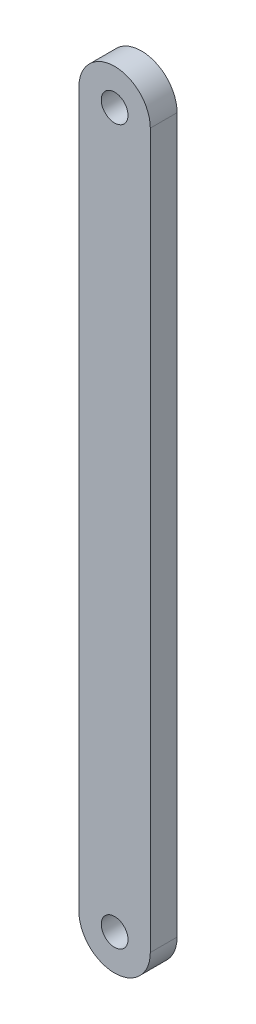
SolidWorks part; units mm, degrees
ref_plane "前基準面" through (0, 0, 0) normal (0, 0, 1) x (1, 0, 0)
ref_plane "上基準面" through (0, 0, 0) normal (0, 1, 0) x (1, 0, 0)
ref_plane "右基準面" through (0, 0, 0) normal (1, 0, 0) x (0, 0, -1)
sketch "Model" plane through (0, 0, 0) normal (0, 0, 1) x (1, 0, 0)
  line L0 (2360.94, 1556.087) -> (2341.94, 1556.087)
  line L1 (2282.5841, 1545.083) -> (2265.648, 1562.019)
  line L2 (2264.9409, 1562.7262) -> (2257.2918, 1570.3752)
  line L3 (2291.9966, 1535.6704) -> (2283.2912, 1544.3759)
  line L4 (2383.2394, 1583.0851) -> (2383.2394, 1591.0855)
  line L5 (2368.4402, 1574.6001) -> (2368.4402, 1566.6001)
  line L6 (2368.4402, 1577.0864) -> (2368.4402, 1575.6001)
  line L7 (2250.4404, 1612.885) -> (2250.4405, 1634.8001)
  line L8 (2250.4403, 1591.1001) -> (2250.4404, 1611.885)
  line L9 (2265.9406, 1588.1) -> (2240.9406, 1588.1001)
  line L10 (2297.9406, 1588.0998) -> (2266.9406, 1588.1)
  line L11 (2190.4406, 1631.8177) -> (2190.4404, 1591.9877)
  line L12 (2190.7401, 1515.6239) -> (2190.7401, 1497.1002)
  line L13 (2190.7401, 1540.2506) -> (2190.7401, 1516.6239)
  line L14 (2190.7401, 1571.1544) -> (2190.7401, 1541.2506)
  line L15 (2190.7401, 1577.1001) -> (2190.7401, 1572.1544)
  line L16 (2198.7401, 1541.6001) -> (2198.7401, 1516.9664)
  line L17 (2198.7401, 1571.0862) -> (2198.7401, 1542.6001)
  line L18 (2206.7401, 1563.7416) -> (2206.7401, 1542.6001)
  line L19 (2206.7401, 1541.6001) -> (2206.7401, 1517.1445)
  line L20 (2367.7339, 1622.5881) -> (2377.2848, 1622.5881)
  line L21 (2378.2848, 1622.5881) -> (2380.2436, 1622.5881)
  line L22 (2170.7403, 1546.4261) -> (2170.7403, 1568.4955)
  line L23 (2170.7403, 1514.0747) -> (2170.7403, 1545.4261)
  line L24 (2182.7403, 1561.7113) -> (2182.7403, 1543.3225)
  line L25 (2182.7403, 1542.3225) -> (2182.7403, 1512.6855)
  line L26 (2402.8405, 1640.5213) -> (2432.7394, 1640.5232)
  line L27 (2310.4404, 1591.078) -> (2310.4432, 1595.6001)
  line L28 (2190.4406, 1634.8004) -> (2190.4406, 1631.8007)
  line L29 (2383.2395, 1620.7452) -> (2383.2395, 1632.084)
  line L30 (2383.2394, 1600.086) -> (2383.2394, 1612.086)
  line L31 (2428.4388, 1546.995) -> (2428.4388, 1524.6001)
  line L32 (2431.4402, 1556.6798) -> (2431.4402, 1567.4449)
  line L33 (2364.4522, 1580.086) -> (2373.94, 1580.086)
  line L34 (2206.7401, 1497.1001) -> (2206.7401, 1516.1445)
  line L35 (2282.8042, 1526.478) -> (2278.5615, 1522.2355)
  line L36 (2278.5615, 1522.2355) -> (2243.8568, 1556.9402)
  line L37 (2243.8568, 1556.9402) -> (2248.0994, 1561.1828)
  line L38 (2248.0994, 1561.1828) -> (2250.2208, 1559.0615)
  line L39 (2250.2208, 1559.0615) -> (2251.635, 1560.4757)
  line L40 (2251.635, 1560.4757) -> (2253.7563, 1558.3544)
  line L41 (2253.7563, 1558.3544) -> (2252.8371, 1557.4352)
  line L42 (2252.8371, 1557.4352) -> (2254.6048, 1555.6674)
  line L43 (2254.6048, 1555.6674) -> (2255.5241, 1556.5867)
  line L44 (2255.5241, 1556.5867) -> (2268.6055, 1543.5052)
  line L45 (2268.6055, 1543.5052) -> (2270.7269, 1545.6265)
  line L46 (2270.7269, 1545.6265) -> (2257.6454, 1558.708)
  line L47 (2257.6454, 1558.708) -> (2258.5646, 1559.6272)
  line L48 (2258.5646, 1559.6272) -> (2256.7968, 1561.395)
  line L49 (2256.7968, 1561.395) -> (2255.8776, 1560.4757)
  line L50 (2255.8776, 1560.4757) -> (2253.7563, 1562.5971)
  line L51 (2253.7563, 1562.5971) -> (2255.1705, 1564.0113)
  line L52 (2255.1705, 1564.0113) -> (2253.0492, 1566.1326)
  line L53 (2253.0492, 1566.1326) -> (2264.3629, 1577.4463)
  line L54 (2264.3629, 1577.4463) -> (2299.0677, 1542.7415)
  line L55 (2299.0677, 1542.7415) -> (2287.754, 1531.4278)
  line L56 (2287.754, 1531.4278) -> (2285.6327, 1533.5491)
  line L57 (2285.6327, 1533.5491) -> (2284.2184, 1532.1349)
  line L58 (2284.2184, 1532.1349) -> (2281.39, 1534.9633)
  line L59 (2281.39, 1534.9633) -> (2282.3093, 1535.8826)
  line L60 (2282.3093, 1535.8826) -> (2280.5415, 1537.6503)
  line L61 (2280.5415, 1537.6503) -> (2279.6223, 1536.7311)
  line L62 (2279.6223, 1536.7311) -> (2279.198, 1537.1554)
  line L63 (2279.198, 1537.1554) -> (2277.0767, 1535.034)
  line L64 (2277.0767, 1535.034) -> (2277.5009, 1534.6098)
  line L65 (2277.5009, 1534.6098) -> (2276.5817, 1533.6905)
  line L66 (2276.5817, 1533.6905) -> (2278.3495, 1531.9228)
  line L67 (2278.3495, 1531.9228) -> (2279.2687, 1532.842)
  line L68 (2279.2687, 1532.842) -> (2282.0971, 1530.0136)
  line L69 (2282.0971, 1530.0136) -> (2280.6829, 1528.5994)
  line L70 (2280.6829, 1528.5994) -> (2282.8042, 1526.478)
  line L71 (2420.0943, 1572.5771) -> (2403.5521, 1576.8112)
  line L72 (2396.9173, 1574.0826) -> (2384.4348, 1577.0916)
  line L73 (2384.4348, 1577.0916) -> (2379.9348, 1577.0881)
  line L74 (2379.9348, 1577.0881) -> (2379.9325, 1580.0881)
  line L75 (2368.4399, 1561.1801) -> (2381.9283, 1561.1801)
  line L76 (2381.9283, 1561.1801) -> (2395.958, 1562.2789)
  line L77 (2402.0756, 1571.0841) -> (2418.6076, 1566.7642)
  line L78 (2425.3801, 1562.2877) -> (2412.2591, 1562.287)
  line L79 (2412.2591, 1562.287) -> (2394.365, 1560.187)
  line L80 (2394.365, 1552.187) -> (2412.3649, 1550.087)
  line L81 (2412.3649, 1550.087) -> (2420.94, 1550.087)
  line L82 (2335.4379, 1586.1907) -> (2341.4379, 1586.1907)
  line L83 (2341.4379, 1586.1907) -> (2341.4379, 1583.1907)
  line L84 (2341.4379, 1583.1907) -> (2353.4379, 1583.1907)
  line L85 (2353.4379, 1583.1907) -> (2353.4379, 1586.1907)
  line L86 (2353.4379, 1586.1907) -> (2359.4375, 1586.1907)
  line L87 (2256.2117, 1499.3305) -> (2276.7178, 1519.8366)
  line L88 (2421.94, 1550.087) -> (2426.9388, 1550.087)
  line L89 (2426.9388, 1550.087) -> (2426.9388, 1547.087)
  line L90 (2426.9388, 1547.087) -> (2428.4388, 1547.087)
  line L91 (2361.94, 1556.087) -> (2374.4388, 1556.087)
  line L92 (2374.4388, 1556.087) -> (2374.4388, 1547.087)
  line L93 (2374.4388, 1547.087) -> (2381.9388, 1547.087)
  line L94 (2381.9388, 1547.087) -> (2381.9388, 1550.087)
  line L95 (2381.9388, 1550.087) -> (2391.9388, 1550.087)
  line L96 (2391.9388, 1550.087) -> (2391.9388, 1547.087)
  line L97 (2391.9388, 1547.087) -> (2402.9388, 1547.087)
  line L98 (2402.9388, 1547.087) -> (2402.9388, 1543.0871)
  line L99 (2402.9388, 1543.0871) -> (2401.6388, 1543.0871)
  line L100 (2401.6388, 1543.0871) -> (2401.6388, 1540.5871)
  line L101 (2401.6388, 1540.5871) -> (2402.9388, 1540.5871)
  line L102 (2402.9388, 1540.5871) -> (2402.9388, 1539.087)
  line L103 (2402.9388, 1539.087) -> (2405.9388, 1539.087)
  line L104 (2405.9388, 1539.087) -> (2405.9388, 1540.5871)
  line L105 (2405.9388, 1540.5871) -> (2407.2388, 1540.5871)
  line L106 (2407.2388, 1540.5871) -> (2407.2388, 1543.0871)
  line L107 (2407.2388, 1543.0871) -> (2405.9388, 1543.0871)
  line L108 (2405.9388, 1543.0871) -> (2405.9388, 1547.087)
  line L109 (2405.9388, 1547.087) -> (2416.9388, 1547.087)
  line L110 (2416.9388, 1547.087) -> (2416.9388, 1550.087)
  line L111 (2310.4464, 1608.3582) -> (2310.467, 1633.5996)
  line L112 (2310.467, 1633.5996) -> (2310.4412, 1635.1138)
  line L113 (2307.986, 1637.7498) -> (2259.9155, 1646.6381)
  line L114 (2255.7293, 1644.7139) -> (2253.9054, 1641.5736)
  line L115 (2359.4374, 1588.5921) -> (2353.4373, 1588.5916)
  line L116 (2353.4373, 1588.5916) -> (2353.4371, 1591.5917)
  line L117 (2352.2968, 1593.5664) -> (2355.8453, 1599.714)
  line L118 (2353.2044, 1605.1909) -> (2347.3559, 1595.0085)
  line L119 (2341.4371, 1591.5907) -> (2341.4374, 1588.5906)
  line L120 (2341.4374, 1588.5906) -> (2335.4373, 1588.5901)
  line L121 (2359.4375, 1586.8452) -> (2359.4375, 1583.0846)
  line L122 (2362.3378, 1580.086) -> (2363.4522, 1580.086)
  line L123 (2374.94, 1580.086) -> (2380.1389, 1580.086)
  line L124 (2434.3958, 1580.0881) -> (2452.2402, 1580.0881)
  line L125 (2452.2402, 1580.0881) -> (2452.2402, 1572.0881)
  line L126 (2452.2402, 1572.0881) -> (2449.2402, 1572.0881)
  line L127 (2449.2402, 1572.0881) -> (2449.2402, 1559.5881)
  line L128 (2449.2402, 1559.5881) -> (2445.2402, 1559.5881)
  line L129 (2445.2402, 1559.5881) -> (2445.2402, 1560.8881)
  line L130 (2445.2402, 1560.8881) -> (2442.2402, 1560.8881)
  line L131 (2442.2402, 1560.8881) -> (2442.2402, 1559.5881)
  line L132 (2442.2402, 1559.5881) -> (2440.2402, 1559.5881)
  line L133 (2440.2402, 1559.5881) -> (2440.2402, 1556.5881)
  line L134 (2440.2402, 1556.5881) -> (2442.2402, 1556.5881)
  line L135 (2442.2402, 1556.5881) -> (2442.2402, 1555.2881)
  line L136 (2442.2402, 1555.2881) -> (2445.2402, 1555.2881)
  line L137 (2445.2402, 1555.2881) -> (2445.2402, 1556.5881)
  line L138 (2445.2402, 1556.5881) -> (2449.2402, 1556.5881)
  line L139 (2449.2402, 1556.5881) -> (2449.2402, 1542.0881)
  line L140 (2449.2402, 1542.0881) -> (2452.2402, 1542.0881)
  line L141 (2452.2402, 1542.0881) -> (2452.2402, 1533.0881)
  line L142 (2452.2402, 1533.0881) -> (2449.0167, 1533.0881)
  line L143 (2445.0402, 1526.0881) -> (2445.0402, 1520.0881)
  line L144 (2445.0402, 1520.0881) -> (2428.4388, 1520.0881)
  line L145 (2386.4827, 1580.0881) -> (2433.3958, 1580.0881)
  line L146 (2368.4378, 1573.3291) -> (2372.4378, 1573.3322)
  line L147 (2372.4378, 1573.3322) -> (2372.4368, 1574.5822)
  line L148 (2372.4368, 1574.5822) -> (2374.9293, 1574.5842)
  line L149 (2374.9293, 1574.5842) -> (2374.9303, 1573.3342)
  line L150 (2374.9303, 1573.3342) -> (2376.9303, 1573.3358)
  line L151 (2376.9303, 1573.3358) -> (2376.9327, 1570.3358)
  line L152 (2376.9327, 1570.3358) -> (2374.9327, 1570.3342)
  line L153 (2374.9327, 1570.3342) -> (2374.9337, 1569.0842)
  line L154 (2374.9337, 1569.0842) -> (2372.4337, 1569.0822)
  line L155 (2372.4337, 1569.0822) -> (2372.4327, 1570.3322)
  line L156 (2372.4327, 1570.3322) -> (2368.4402, 1570.3291)
  line L157 (2238.534, 1517.0082) -> (2259.0401, 1537.5143)
  line L158 (2241.3624, 1555.1919) -> (2220.8563, 1534.6858)
  line L159 (2428.4402, 1527.5881) -> (2431.4402, 1527.5881)
  line L160 (2431.4402, 1527.5881) -> (2431.4402, 1540.5881)
  line L161 (2431.4402, 1540.5881) -> (2435.4402, 1540.5881)
  line L162 (2435.4402, 1540.5881) -> (2435.4402, 1539.2881)
  line L163 (2435.4402, 1539.2881) -> (2438.4402, 1539.2881)
  line L164 (2438.4402, 1539.2881) -> (2438.4402, 1540.5881)
  line L165 (2438.4402, 1540.5881) -> (2440.4402, 1540.5881)
  line L166 (2440.4402, 1540.5881) -> (2440.4402, 1543.5881)
  line L167 (2440.4402, 1543.5881) -> (2438.4402, 1543.5881)
  line L168 (2438.4402, 1543.5881) -> (2438.4402, 1544.8881)
  line L169 (2438.4402, 1544.8881) -> (2435.4402, 1544.8881)
  line L170 (2435.4402, 1544.8881) -> (2435.4402, 1543.5881)
  line L171 (2435.4402, 1543.5881) -> (2431.4402, 1543.5881)
  line L172 (2431.4402, 1543.5881) -> (2431.4402, 1555.6798)
  line L173 (2431.4402, 1568.4449) -> (2431.4402, 1575.0881)
  line L174 (2431.4402, 1575.0881) -> (2428.4402, 1575.0881)
  line L175 (2428.4402, 1575.0881) -> (2428.4402, 1580.0881)
  line L176 (2257.9403, 1595.8) -> (2257.9403, 1598.8)
  line L177 (2257.9403, 1598.8) -> (2267.9403, 1598.8)
  line L178 (2267.9403, 1598.8) -> (2267.9403, 1595.8)
  line L179 (2267.9403, 1595.8) -> (2257.9403, 1595.8)
  line L180 (2260.6167, 1627.8) -> (2260.6166, 1617.8)
  line L181 (2260.6166, 1617.8) -> (2257.6166, 1617.8001)
  line L182 (2257.6166, 1617.8001) -> (2257.6167, 1627.8001)
  line L183 (2257.6167, 1627.8001) -> (2260.6167, 1627.8)
  line L184 (2240.2641, 1598.1001) -> (2240.2642, 1608.1001)
  line L185 (2240.2642, 1608.1001) -> (2243.2642, 1608.1001)
  line L186 (2243.2642, 1608.1001) -> (2243.2641, 1598.1001)
  line L187 (2243.2641, 1598.1001) -> (2240.2641, 1598.1001)
  line L188 (2158.7403, 1580.4001) -> (2158.7403, 1500.4)
  line L189 (2170.7403, 1500.4) -> (2170.7403, 1513.0747)
  line L190 (2170.7403, 1569.4955) -> (2170.7403, 1580.4)
  line L191 (2368.4348, 1577.079) -> (2369.9348, 1577.0802)
  line L192 (2369.9348, 1577.0802) -> (2369.9325, 1580.0802)
  line L193 (2242.4043, 1648.5707) -> (2168.1294, 1646.9241)
  line L194 (2168.7764, 1638.795) -> (2186.8708, 1638.8729)
  line L195 (2186.8708, 1638.8729) -> (2242.5211, 1639.1123)
  line L196 (2410.365, 1556.937) -> (2415.365, 1556.937)
  line L197 (2415.365, 1555.437) -> (2410.365, 1555.437)
  line L198 (2304.4403, 1614.7998) -> (2307.4404, 1614.7998)
  line L199 (2307.4404, 1614.7998) -> (2307.4403, 1608.7998)
  line L200 (2307.4403, 1608.7998) -> (2304.4403, 1608.7998)
  line L201 (2304.4403, 1608.7998) -> (2304.4403, 1614.7998)
  line L202 (2301.4404, 1631.7998) -> (2278.4404, 1631.7999)
  line L203 (2278.4404, 1631.7999) -> (2278.4404, 1619.7999)
  line L204 (2278.4404, 1619.7999) -> (2301.4404, 1619.7998)
  line L205 (2301.4404, 1619.7998) -> (2301.4404, 1631.7998)
  line L206 (2307.4403, 1601.7998) -> (2307.4403, 1595.7998)
  line L207 (2307.4403, 1595.7998) -> (2304.4403, 1595.7998)
  line L208 (2304.4403, 1595.7998) -> (2304.4403, 1601.7998)
  line L209 (2304.4403, 1601.7998) -> (2307.4403, 1601.7998)
  line L210 (2302.9403, 1595.7998) -> (2302.9403, 1598.7998)
  line L211 (2302.9403, 1598.7998) -> (2292.9403, 1598.7999)
  line L212 (2292.9403, 1598.7999) -> (2292.9403, 1595.7999)
  line L213 (2292.9403, 1595.7999) -> (2302.9403, 1595.7998)
  line L214 (2239.9406, 1588.1001) -> (2193.4403, 1588.1004)
  line L215 (2190.4403, 1591.1004) -> (2190.4404, 1591.9877)
  line L216 (2253.4032, 1640.7089) -> (2250.8464, 1636.3069)
  line L217 (2246.9406, 1637.8001) -> (2193.4406, 1637.8004)
  line L218 (2190.4406, 1634.8004) -> (2190.4406, 1634.8033)
  line L219 (2242.9405, 1630.1001) -> (2232.9405, 1630.1002)
  line L220 (2232.9405, 1630.1002) -> (2232.9405, 1627.1002)
  line L221 (2232.9405, 1627.1002) -> (2242.9405, 1627.1001)
  line L222 (2242.9405, 1627.1001) -> (2242.9405, 1630.1001)
  line L223 (2207.9405, 1630.1003) -> (2197.9405, 1630.1004)
  line L224 (2197.9405, 1630.1004) -> (2197.9405, 1627.1004)
  line L225 (2197.9405, 1627.1004) -> (2207.9405, 1627.1003)
  line L226 (2207.9405, 1627.1003) -> (2207.9405, 1630.1003)
  line L227 (2222.4404, 1606.1002) -> (2199.4404, 1606.1003)
  line L228 (2199.4404, 1606.1003) -> (2199.4404, 1594.1003)
  line L229 (2199.4404, 1594.1003) -> (2222.4404, 1594.1002)
  line L230 (2222.4404, 1594.1002) -> (2222.4404, 1606.1002)
  line L231 (2196.4405, 1624.1004) -> (2193.4405, 1624.1004)
  line L232 (2193.4405, 1624.1004) -> (2193.4405, 1630.1004)
  line L233 (2193.4405, 1630.1004) -> (2196.4405, 1630.1004)
  line L234 (2196.4405, 1630.1004) -> (2196.4405, 1624.1004)
  line L235 (2196.4404, 1611.1004) -> (2193.4404, 1611.1004)
  line L236 (2193.4404, 1611.1004) -> (2193.4405, 1617.1004)
  line L237 (2193.4405, 1617.1004) -> (2196.4405, 1617.1004)
  line L238 (2196.4405, 1617.1004) -> (2196.4404, 1611.1004)
  line L239 (2320.4402, 1592.1001) -> (2316.9402, 1592.1001)
  line L240 (2316.9402, 1592.1001) -> (2316.9402, 1569.1001)
  line L241 (2316.9402, 1569.1001) -> (2328.9402, 1569.1001)
  line L242 (2328.9402, 1569.1001) -> (2328.9402, 1592.1001)
  line L243 (2328.9402, 1592.1001) -> (2325.4402, 1592.1001)
  line L244 (2325.4402, 1592.1001) -> (2325.4402, 1594.1002)
  line L245 (2325.4402, 1594.1002) -> (2320.4402, 1594.1002)
  line L246 (2320.4402, 1594.1002) -> (2320.4402, 1592.1001)
  line L247 (2251.2619, 1508.5229) -> (2253.7368, 1506.048)
  line L248 (2253.7368, 1506.048) -> (2270.0002, 1522.3115)
  line L249 (2270.0002, 1522.3115) -> (2261.515, 1530.7968)
  line L250 (2261.515, 1530.7968) -> (2245.2515, 1514.5333)
  line L251 (2245.2515, 1514.5333) -> (2247.7264, 1512.0584)
  line L252 (2247.7264, 1512.0584) -> (2246.3121, 1510.6441)
  line L253 (2246.3121, 1510.6441) -> (2249.8476, 1507.1086)
  line L254 (2249.8476, 1507.1086) -> (2251.2619, 1508.5229)
  line L255 (2233.5842, 1526.2006) -> (2236.0591, 1523.7257)
  line L256 (2236.0591, 1523.7257) -> (2252.3226, 1539.9891)
  line L257 (2252.3226, 1539.9891) -> (2243.8373, 1548.4744)
  line L258 (2243.8373, 1548.4744) -> (2227.5738, 1532.211)
  line L259 (2227.5738, 1532.211) -> (2230.0487, 1529.7361)
  line L260 (2230.0487, 1529.7361) -> (2228.6344, 1528.3218)
  line L261 (2228.6344, 1528.3218) -> (2232.17, 1524.7863)
  line L262 (2232.17, 1524.7863) -> (2233.5842, 1526.2006)
  line L263 (2198.7401, 1515.9664) -> (2198.7401, 1497.1001)
  line L264 (2198.7401, 1572.0862) -> (2198.7401, 1577.1001)
  line L265 (2175.2403, 1516.6002) -> (2175.2403, 1509.1002)
  line L266 (2175.2403, 1509.1002) -> (2178.2403, 1509.1002)
  line L267 (2178.2403, 1509.1002) -> (2178.2403, 1516.6002)
  line L268 (2178.2403, 1516.6002) -> (2175.2403, 1516.6002)
  line L269 (2175.2403, 1569.1002) -> (2175.2403, 1564.1002)
  line L270 (2175.2403, 1564.1002) -> (2178.2403, 1564.1002)
  line L271 (2178.2403, 1564.1002) -> (2178.2403, 1569.1002)
  line L272 (2178.2403, 1569.1002) -> (2175.2403, 1569.1002)
  line L273 (2163.2403, 1562.4) -> (2166.2403, 1562.4)
  line L274 (2166.2403, 1562.4) -> (2166.2403, 1570.4)
  line L275 (2166.2403, 1570.4) -> (2163.2403, 1570.4)
  line L276 (2163.2403, 1570.4) -> (2163.2403, 1562.4)
  line L277 (2163.2403, 1532.4) -> (2166.2403, 1532.4)
  line L278 (2166.2403, 1532.4) -> (2166.2403, 1523.4)
  line L279 (2166.2403, 1523.4) -> (2163.2403, 1523.4)
  line L280 (2163.2403, 1523.4) -> (2163.2403, 1532.4)
  line L281 (2182.7403, 1562.7113) -> (2182.7403, 1579.1002)
  line L282 (2182.7403, 1511.6855) -> (2182.7403, 1499.1001)
  line L283 (2206.7401, 1564.7416) -> (2206.7401, 1577.1001)
  line L284 (2434.7402, 1574.5881) -> (2434.7402, 1566.3381)
  line L285 (2436.7402, 1564.3382) -> (2443.7402, 1564.3382)
  line L286 (2445.7402, 1566.3381) -> (2445.7402, 1574.5881)
  line L287 (2443.2402, 1577.0881) -> (2437.2402, 1577.0881)
  line L288 (2271.2218, 1535.9391) -> (2278.2928, 1543.0101)
  line L289 (2278.2928, 1543.0101) -> (2276.1715, 1545.1315)
  line L290 (2276.1715, 1545.1315) -> (2269.1005, 1538.0605)
  line L291 (2269.1005, 1538.0605) -> (2271.2218, 1535.9391)
  line L292 (2163.9903, 1515.4) -> (2163.9903, 1510.4)
  line L293 (2165.4903, 1510.4) -> (2165.4903, 1515.4)
  line L294 (2277.9403, 1606.8) -> (2277.9403, 1600.8)
  line L295 (2277.9403, 1600.8) -> (2267.9403, 1600.8)
  line L296 (2267.9403, 1600.8) -> (2267.9403, 1606.8)
  line L297 (2267.9403, 1606.8) -> (2277.9403, 1606.8)
  line L298 (2313.4402, 1563.1001) -> (2332.4402, 1563.1001)
  line L299 (2335.4402, 1566.1001) -> (2335.4402, 1569.6001)
  line L300 (2335.4402, 1570.6001) -> (2335.4402, 1595.1001)
  line L301 (2332.4402, 1598.1001) -> (2320.9401, 1598.1001)
  line L302 (2310.4402, 1595.1001) -> (2310.4402, 1578.1001)
  line L303 (2365.2395, 1629.0842) -> (2365.2394, 1632.0842)
  line L304 (2365.2394, 1632.0842) -> (2359.2394, 1632.0842)
  line L305 (2359.2394, 1632.0842) -> (2359.2394, 1634.4843)
  line L306 (2359.2394, 1634.4843) -> (2365.2394, 1634.4842)
  line L307 (2365.2394, 1634.4842) -> (2365.2396, 1637.4843)
  line L308 (2365.2396, 1637.4843) -> (2377.2395, 1637.4841)
  line L309 (2377.2395, 1637.4841) -> (2377.2395, 1634.484)
  line L310 (2377.2395, 1634.484) -> (2383.2395, 1634.484)
  line L311 (2377.2388, 1594.586) -> (2377.2388, 1617.386)
  line L312 (2377.2388, 1617.386) -> (2365.2379, 1617.386)
  line L313 (2365.2379, 1617.386) -> (2365.2379, 1594.586)
  line L314 (2365.2379, 1594.586) -> (2377.2388, 1594.586)
  line L315 (2419.5574, 1621.7062) -> (2407.3574, 1621.7062)
  line L316 (2407.3574, 1621.7062) -> (2407.3574, 1598.9062)
  line L317 (2407.3574, 1598.9062) -> (2419.5574, 1598.9062)
  line L318 (2419.5574, 1598.9062) -> (2419.5574, 1621.7062)
  line L319 (2363.4402, 1570.6886) -> (2364.9402, 1570.6886)
  line L320 (2364.9402, 1570.6886) -> (2364.9402, 1565.6886)
  line L321 (2364.9402, 1565.6886) -> (2363.4402, 1565.6886)
  line L322 (2363.4402, 1565.6886) -> (2363.4402, 1561.9886)
  line L323 (2363.4402, 1561.9886) -> (2340.6402, 1561.9886)
  line L324 (2340.6402, 1561.9886) -> (2340.6402, 1574.1886)
  line L325 (2340.6402, 1574.1886) -> (2363.4402, 1574.1886)
  line L326 (2363.4402, 1574.1886) -> (2363.4402, 1570.6886)
  line L327 (2383.2394, 1592.0855) -> (2383.2394, 1600.086)
  line L328 (2383.2394, 1600.086) -> (2380.2394, 1600.086)
  line L329 (2380.2394, 1600.086) -> (2380.2394, 1612.086)
  line L330 (2380.2394, 1612.086) -> (2383.2394, 1612.086)
  line L331 (2383.2394, 1612.086) -> (2383.2394, 1615.4156)
  line L332 (2443.6753, 1583.3062) -> (2443.6753, 1637.3063)
  line L333 (2359.4375, 1619.7446) -> (2359.4375, 1612.086)
  line L334 (2359.4375, 1612.086) -> (2362.4378, 1612.086)
  line L335 (2362.4378, 1612.086) -> (2362.4378, 1600.086)
  line L336 (2362.4378, 1600.086) -> (2359.4375, 1600.086)
  line L337 (2359.4375, 1600.086) -> (2359.4375, 1587.8452)
  line L338 (2383.2394, 1616.4156) -> (2383.2394, 1619.7452)
  line L339 (2362.3273, 1580.0864) -> (2357.9402, 1580.0864)
  line L340 (2357.9402, 1580.0864) -> (2357.9402, 1577.0866)
  line L341 (2357.9402, 1577.0866) -> (2345.9402, 1577.0866)
  line L342 (2345.9402, 1577.0866) -> (2345.9402, 1580.0864)
  line L343 (2345.9402, 1580.0864) -> (2338.283, 1580.0864)
  line L344 (2310.4402, 1572.4685) -> (2310.4402, 1578.1001)
  line L345 (2216.7403, 1493.1001) -> (2300.4403, 1493.1001)
  line L346 (2335.4402, 1567.8863) -> (2335.4402, 1559.0824)
  line L347 (2432.7394, 1640.5232) -> (2440.2394, 1640.5237)
  line L348 (2440.2391, 1648.523) -> (2366.5, 1649.4883)
  line L349 (2353.9672, 1649.5484) -> (2325.1508, 1649.2724)
  line L350 (2325.0987, 1641.2736) -> (2353.9091, 1640.6221)
  line L351 (2366.4416, 1640.519) -> (2402.8405, 1640.5213)
  line L352 (2383.2394, 1637.3062) -> (2383.2394, 1633.784)
  line L353 (2379.7394, 1629.0847) -> (2371.8744, 1629.0843)
  line L354 (2370.8744, 1629.0843) -> (2357.7394, 1629.0836)
  line L355 (2357.7394, 1622.5881) -> (2366.7339, 1622.5881)
  line L356 (2357.9402, 1556.0866) -> (2357.9402, 1559.0866)
  line L357 (2357.9402, 1559.0866) -> (2345.9402, 1559.0866)
  line L358 (2345.9402, 1559.0866) -> (2345.9402, 1556.0866)
  line L359 (2310.4459, 1594.5943) -> (2310.4404, 1601.0998)
  line L360 (2310.4404, 1601.0998) -> (2310.4456, 1607.3582)
  line L361 (2298.9406, 1588.0998) -> (2307.4402, 1588.0998)
  line L362 (2383.2394, 1632.784) -> (2383.2395, 1632.084)
  line L363 (2383.2395, 1632.084) -> (2377.2395, 1632.0842)
  line L364 (2377.2395, 1632.0842) -> (2377.2394, 1629.0841)
  line L365 (2411.244, 1571.103) -> (2416.0906, 1569.8535)
  line L366 (2416.4211, 1571.1108) -> (2411.5746, 1572.3603)
  line L367 (2368.4402, 1559.0824) -> (2368.4402, 1565.6001)
  line L368 (2310.4402, 1571.4685) -> (2310.4402, 1499.9993)
  line L369 (2315.7188, 1495.007) -> (2374.4388, 1495.007)
  line L370 (2374.4388, 1495.007) -> (2374.4388, 1504.007)
  line L371 (2374.4388, 1504.007) -> (2381.9388, 1504.007)
  line L372 (2381.9388, 1504.007) -> (2381.9388, 1501.007)
  line L373 (2381.9388, 1501.007) -> (2391.9388, 1501.007)
  line L374 (2391.9388, 1501.007) -> (2391.9388, 1504.007)
  line L375 (2391.9388, 1504.007) -> (2402.9388, 1504.007)
  line L376 (2402.9388, 1504.007) -> (2402.9388, 1508.007)
  line L377 (2402.9388, 1508.007) -> (2401.6388, 1508.007)
  line L378 (2401.6388, 1508.007) -> (2401.6388, 1510.507)
  line L379 (2401.6388, 1510.507) -> (2402.9388, 1510.507)
  line L380 (2402.9388, 1510.507) -> (2402.9388, 1512.007)
  line L381 (2402.9388, 1512.007) -> (2405.9388, 1512.007)
  line L382 (2405.9388, 1512.007) -> (2405.9388, 1510.507)
  line L383 (2405.9388, 1510.507) -> (2407.2388, 1510.507)
  line L384 (2407.2388, 1510.507) -> (2407.2388, 1508.007)
  line L385 (2407.2388, 1508.007) -> (2405.9388, 1508.007)
  line L386 (2405.9388, 1508.007) -> (2405.9388, 1504.007)
  line L387 (2405.9388, 1504.007) -> (2416.9388, 1504.007)
  line L388 (2416.9388, 1504.007) -> (2416.9388, 1501.007)
  line L389 (2416.9388, 1501.007) -> (2426.9388, 1501.007)
  line L390 (2426.9388, 1501.007) -> (2426.9388, 1504.007)
  line L391 (2426.9388, 1504.007) -> (2428.4388, 1504.007)
  line L392 (2428.4388, 1504.007) -> (2428.4388, 1523.6001)
  line L393 (2340.94, 1556.087) -> (2315.7188, 1556.087)
  line L394 (2227.4992, 1523.8003) -> (2244.7831, 1506.5164)
  line L395 (2245.4902, 1505.8093) -> (2253.6406, 1497.6589)
  line L396 (2263.5401, 1497.6589) -> (2282.8893, 1517.0082)
  line L397 (2282.8893, 1517.0082) -> (2301.5315, 1535.6503)
  line L398 (2301.5315, 1545.5498) -> (2263.5401, 1583.5412)
  line L399 (2253.6406, 1583.5412) -> (2234.9985, 1564.899)
  line L400 (2234.9985, 1564.899) -> (2215.6492, 1545.5498)
  line L401 (2215.6492, 1535.6503) -> (2226.7921, 1524.5074)
  line L402 (2246.9406, 1637.8001) -> (2247.4404, 1637.8001)
  line L403 (2253.4032, 1640.7089) -> (2253.9054, 1641.5736)
  line L404 (2182.7403, 1497.1002) -> (2182.7403, 1499.1001)
  line L405 (2170.7403, 1499.1002) -> (2170.7403, 1500.4)
  line L406 (2170.7403, 1569.4955) -> (2170.7403, 1568.4955)
  line L407 (2170.7403, 1546.4261) -> (2170.7403, 1545.4261)
  line L408 (2170.7403, 1514.0747) -> (2170.7403, 1513.0747)
  line L409 (2182.7403, 1511.6855) -> (2182.7403, 1512.6855)
  line L410 (2182.7403, 1542.3225) -> (2182.7403, 1543.3225)
  line L411 (2182.7403, 1561.7113) -> (2182.7403, 1562.7113)
  line L412 (2190.7401, 1572.1544) -> (2190.7401, 1571.1544)
  line L413 (2190.7401, 1541.2506) -> (2190.7401, 1540.2506)
  line L414 (2190.7401, 1516.6239) -> (2190.7401, 1515.6239)
  line L415 (2198.7401, 1515.9664) -> (2198.7401, 1516.9664)
  line L416 (2198.7401, 1541.6001) -> (2198.7401, 1542.6001)
  line L417 (2198.7401, 1571.0862) -> (2198.7401, 1572.0862)
  line L418 (2206.7401, 1564.7416) -> (2206.7401, 1563.7416)
  line L419 (2206.7401, 1542.6001) -> (2206.7401, 1541.6001)
  line L420 (2206.7401, 1517.1445) -> (2206.7401, 1516.1445)
  line L421 (2239.9406, 1588.1001) -> (2240.9406, 1588.1001)
  line L422 (2265.9406, 1588.1) -> (2266.9406, 1588.1)
  line L423 (2250.4404, 1612.885) -> (2250.4404, 1611.885)
  line L424 (2297.9406, 1588.0998) -> (2298.9406, 1588.0998)
  line L425 (2310.4456, 1607.3582) -> (2310.4464, 1608.3582)
  line L426 (2383.2394, 1633.784) -> (2383.2394, 1632.784)
  line L427 (2383.2394, 1616.4156) -> (2383.2394, 1615.4156)
  line L428 (2370.8744, 1629.0843) -> (2371.8744, 1629.0843)
  line L429 (2366.7339, 1622.5881) -> (2367.7339, 1622.5881)
  line L430 (2377.2848, 1622.5881) -> (2378.2848, 1622.5881)
  line L431 (2383.2394, 1592.0855) -> (2383.2394, 1591.0855)
  line L432 (2363.4522, 1580.086) -> (2364.4522, 1580.086)
  line L433 (2373.94, 1580.086) -> (2374.94, 1580.086)
  line L434 (2433.3958, 1580.0881) -> (2434.3958, 1580.0881)
  line L435 (2359.4375, 1587.8452) -> (2359.4375, 1586.8452)
  line L436 (2319.94, 1598.1001) -> (2320.9401, 1598.1001)
  line L437 (2310.4402, 1572.4685) -> (2310.4402, 1571.4685)
  line L438 (2264.9409, 1562.7262) -> (2265.648, 1562.019)
  line L439 (2282.5841, 1545.083) -> (2283.2912, 1544.3759)
  line L440 (2226.7921, 1524.5074) -> (2227.4992, 1523.8003)
  line L441 (2244.7831, 1506.5164) -> (2245.4902, 1505.8093)
  line L442 (2335.4402, 1570.6001) -> (2335.4402, 1569.6001)
  line L443 (2340.94, 1556.087) -> (2341.94, 1556.087)
  line L444 (2368.4402, 1575.6001) -> (2368.4402, 1574.6001)
  line L445 (2368.4402, 1566.6001) -> (2368.4402, 1565.6001)
  line L446 (2360.94, 1556.087) -> (2361.94, 1556.087)
  line L447 (2431.4402, 1568.4449) -> (2431.4402, 1567.4449)
  line L448 (2431.4402, 1556.6798) -> (2431.4402, 1555.688)
  line L449 (2420.94, 1550.087) -> (2421.94, 1550.087)
  line L450 (2428.4388, 1523.6001) -> (2428.4388, 1524.6001)
  line L451 (2313.4402, 1598.1001) -> (2319.94, 1598.1001)
  circle A0 centre (2362.7174, 1498.047) radius 1.5
  circle A1 centre (2402.8138, 1573.9477) radius 1.25
  circle A2 centre (2339.7174, 1498.047) radius 1.5
  circle A3 centre (2369.0388, 1508.507) radius 1.3
  circle A4 centre (2362.7174, 1553.047) radius 1.5
  circle A5 centre (2339.7174, 1553.047) radius 1.5
  circle A6 centre (2424.9388, 1508.507) radius 1.3
  circle A7 centre (2380.2895, 1583.0852) radius 1.5
  circle A8 centre (2424.9388, 1527.307) radius 1.3
  circle A9 centre (2369.0388, 1527.307) radius 1.3
  circle A10 centre (2440.4574, 1583.3059) radius 1.25
  circle A11 centre (2352.7174, 1553.047) radius 0.75
  circle A12 centre (2314.4374, 1499.317) radius 1.5
  circle A13 centre (2393.3388, 1525.2267) radius 0.75
  circle A14 centre (2404.3389, 1531.937) radius 0.75
  circle A15 centre (2404.3389, 1518.537) radius 0.75
  circle A16 centre (2280.4404, 1597.2999) radius 1.5
  circle A17 centre (2339.1844, 1530.697) radius 0.75
  circle A18 centre (2423.1888, 1533.707) radius 1.5
  circle A19 centre (2379.7394, 1592.5859) radius 1.25
  circle A20 centre (2415.3389, 1525.2371) radius 0.75
  circle A21 centre (2404.4574, 1610.3062) radius 1.25
  circle A22 centre (2395.4418, 1568.2003) radius 1.3
  circle A23 centre (2379.7394, 1619.7881) radius 1.25
  circle A24 centre (2440.4574, 1637.3059) radius 1.25
  circle A25 centre (2362.738, 1619.7881) radius 1.25
  circle A26 centre (2386.4574, 1637.3059) radius 1.25
  circle A27 centre (2362.738, 1592.5859) radius 1.25
  circle A28 centre (2422.4574, 1610.3062) radius 1.25
  circle A29 centre (2362.1881, 1583.0852) radius 1.5
  circle A30 centre (2386.4574, 1583.3059) radius 1.25
  circle A31 centre (2176.7403, 1531.1001) radius 1.5
  circle A32 centre (2176.7435, 1499.1072) radius 1.5
  circle A33 centre (2176.7403, 1579.1002) radius 1.25
  circle A34 centre (2164.7403, 1500.4) radius 3.6
  circle A35 centre (2164.7403, 1580.4) radius 1.25
  circle A36 centre (2202.7401, 1577.1001) radius 1.5
  circle A37 centre (2202.7401, 1497.1001) radius 1.5
  circle A38 centre (2194.7401, 1497.1001) radius 1.5
  circle A39 centre (2186.7403, 1497.1002) radius 1.25
  circle A40 centre (2186.7403, 1577.1002) radius 1.5
  circle A41 centre (2360.1884, 1645.0446) radius 1.5
  circle A42 centre (2168.218, 1642.925) radius 1.5
  circle A43 centre (2440.1867, 1644.5234) radius 1.5
  circle A44 centre (2425.9396, 1567.9855) radius 3.6
  circle A45 centre (2394.365, 1556.187) radius 1.25
  circle A46 centre (2425.3649, 1556.1871) radius 3.6
  circle A47 centre (2289.9407, 1634.7999) radius 1.25
  circle A48 centre (2289.9404, 1616.7999) radius 1.25
  circle A49 centre (2259.1882, 1642.7048) radius 1.25
  circle A50 centre (2305.9403, 1605.2998) radius 1.5
  circle A51 centre (2231.5904, 1513.6001) radius 1.5
  circle A52 centre (2300.4403, 1578.1001) radius 1.5
  circle A53 centre (2300.4403, 1503.1001) radius 1.5
  circle A54 centre (2216.7828, 1578.1001) radius 1.5
  circle A55 centre (2216.7403, 1503.1001) radius 1.5
  circle A56 centre (2285.5904, 1513.6001) radius 1.5
  circle A57 centre (2347.4375, 1587.3912) radius 1.25
  circle A58 centre (2231.5904, 1567.6001) radius 1.5
  circle A59 centre (2357.4361, 1604.7124) radius 1.25
  circle A60 centre (2186.4397, 1632.1023) radius 1.25
  circle A61 centre (2166.5157, 1590.3594) radius 1.5
  circle A62 centre (2186.4396, 1592.1023) radius 1.5
  circle A63 centre (2404.3389, 1525.2371) radius 1.5
  circle A64 centre (2285.5904, 1567.6001) radius 1.5
  circle A65 centre (2313.9402, 1580.6001) radius 1.5
  circle A66 centre (2263.9898, 1512.0584) radius 1.5
  circle A67 centre (2246.3122, 1529.7361) radius 1.5
  circle A68 centre (2331.9402, 1580.6001) radius 1.5
  circle A69 centre (2251.2619, 1524.7863) radius 1.5
  circle A70 centre (2233.5842, 1542.464) radius 1.5
  circle A71 centre (2220.4405, 1628.6002) radius 1.5
  circle A72 centre (2210.9403, 1591.1003) radius 1.25
  circle A73 centre (2210.9404, 1609.1003) radius 1.25
  circle A74 centre (2194.9405, 1620.6004) radius 1.5
  circle A75 centre (2338.2401, 1576.5867) radius 1.5
  circle A76 centre (2338.2401, 1559.5866) radius 1.5
  circle A77 centre (2365.4402, 1576.5866) radius 1.5
  circle A78 centre (2365.4401, 1559.5866) radius 1.5
  circle A79 centre (2194.7402, 1577.1001) radius 1.5
  circle A80 centre (2371.2395, 1633.2842) radius 1.25
  circle A81 centre (2164.7403, 1548.4001) radius 1.5
  circle A82 centre (2379.7394, 1625.8358) radius 1.5
  circle A83 centre (2357.7394, 1625.8358) radius 1.5
  arc A84 (2190.7401, 1577.1001) -> (2182.7403, 1577.1003) centre (2186.7402, 1577.1002) ccw
  arc A85 (2190.2118, 1630.7714) -> (2190.34, 1593.0001) centre (2243.8021, 1612.0675) ccw
  circle A86 centre (2325.2154, 1645.2794) radius 1.25
  circle A87 centre (2248.2119, 1643.9126) radius 1.5
  arc A88 (2247.6538, 1637.8598) -> (2253.2388, 1640.8043) centre (2248.0666, 1643.8459) ccw
  arc A89 (2176.2409, 1585.0794) -> (2170.7403, 1579.1002) centre (2176.7403, 1579.1002) ccw
  arc A90 (2216.7403, 1588.1001) -> (2206.7403, 1579.1001) centre (2216.7829, 1577.9973) ccw
  arc A91 (2166.2647, 1586.3672) -> (2169.1221, 1587.3251) centre (2166.5157, 1590.3593) ccw
  circle A92 centre (2325.7174, 1553.047) radius 0.75
  circle A93 centre (2329.6874, 1550.117) radius 1.5
  circle A94 centre (2357.6174, 1550.117) radius 1.5
  arc A95 (2407.9042, 1525.7355) -> (2407.9042, 1524.7387) centre (2404.3389, 1525.2371) ccw
  arc A96 (2368.4402, 1577.0906) -> (2365.5974, 1580.0864) centre (2365.4403, 1577.0906) ccw
  arc A97 (2234.2914, 1517.0082) -> (2238.534, 1517.0082) centre (2236.4127, 1519.1295) ccw
  arc A98 (2263.2827, 1537.5143) -> (2259.0401, 1537.5143) centre (2261.1614, 1535.3929) ccw
  arc A99 (2380.2394, 1580.0881) -> (2383.2394, 1583.0881) centre (2380.2392, 1583.0883) ccw
  arc A100 (2198.7401, 1497.1001) -> (2206.7401, 1497.1001) centre (2202.7401, 1497.1001) ccw
  arc A101 (2400.6101, 1571.9757) -> (2402.0756, 1571.0841) centre (2402.8138, 1573.9477) ccw
  arc A102 (2426.748, 1562.4593) -> (2431.4126, 1567.4456) centre (2425.8814, 1567.9449) ccw
  arc A103 (2431.4198, 1556.6869) -> (2426.6747, 1562.14) centre (2425.3398, 1556.1874) ccw
  arc A104 (2190.2118, 1630.7714) -> (2190.4406, 1631.8007) centre (2186.4321, 1632.1515) ccw
  arc A105 (2246.9678, 1638.0429) -> (2247.6538, 1637.8598) centre (2248.8756, 1643.8142) ccw
  arc A106 (2253.2388, 1640.8043) -> (2253.6717, 1641.7045) centre (2248.1668, 1643.7977) ccw
  arc A107 (2165.2848, 1586.5534) -> (2166.2647, 1586.3672) centre (2166.5157, 1590.3594) ccw
  arc A108 (2166.2287, 1586.2125) -> (2165.2438, 1586.3789) centre (2164.7403, 1580.4) ccw
  arc A109 (2177.2398, 1585.0794) -> (2176.2409, 1585.0794) centre (2176.7403, 1579.1002) ccw
  arc A110 (2190.4404, 1591.9877) -> (2190.34, 1593.0001) centre (2186.4396, 1592.1025) ccw
  arc A111 (2206.7403, 1579.1001) -> (2206.7401, 1577.1001) centre (2216.7829, 1578.0991) ccw
  arc A112 (2400.2899, 1571.8355) -> (2399.6299, 1572.5851) centre (2395.4243, 1568.217) ccw
  arc A113 (2400.0807, 1572.8184) -> (2400.6101, 1571.9757) centre (2402.8138, 1573.9477) ccw
  arc A114 (2425.7515, 1562.3928) -> (2426.7495, 1562.4485) centre (2425.9396, 1567.9855) ccw
  arc A115 (2431.4126, 1567.4456) -> (2431.4126, 1568.4442) centre (2425.9431, 1567.9449) ccw
  arc A116 (2431.4198, 1555.688) -> (2431.4198, 1556.6869) centre (2425.3649, 1556.1874) ccw
  arc A117 (2426.6747, 1562.14) -> (2425.6854, 1562.278) centre (2425.34, 1556.1885) ccw
  arc A118 (2407.9042, 1524.7387) -> (2407.9042, 1525.7355) centre (2404.3389, 1525.2371) ccw
  arc A119 (2425.3649, 1550.087) -> (2427.0554, 1550.3332) centre (2425.3399, 1556.1873) ccw
  arc A120 (2425.3649, 1550.087) -> (2431.4198, 1555.688) centre (2425.3398, 1556.1874) ccw
  arc A121 (2431.4126, 1568.4442) -> (2427.2701, 1573.3222) centre (2425.8814, 1567.9449) ccw
  arc A122 (2427.2701, 1573.3222) -> (2423.5266, 1572.928) centre (2426.0083, 1567.3323) ccw
  arc A123 (2420.0943, 1572.5771) -> (2423.5266, 1572.928) centre (2421.3332, 1577.421) ccw
  arc A124 (2403.5521, 1576.8112) -> (2400.0807, 1572.8184) centre (2402.8138, 1573.9477) ccw
  arc A125 (2399.6299, 1572.5851) -> (2396.9173, 1574.0826) centre (2395.4722, 1568.2592) ccw
  arc A126 (2395.958, 1562.2789) -> (2401.4713, 1568.155) centre (2394.8726, 1568.8217) ccw
  arc A127 (2401.4713, 1568.155) -> (2400.2899, 1571.8355) centre (2395.4722, 1568.2592) ccw
  arc A128 (2421.45, 1564.8084) -> (2418.6076, 1566.7642) centre (2417.3686, 1561.9201) ccw
  arc A129 (2421.45, 1564.8084) -> (2425.4678, 1562.4067) centre (2426.7135, 1569.0521) ccw
  arc A130 (2425.4678, 1562.4067) -> (2425.7515, 1562.3928) centre (2425.8814, 1567.9449) ccw
  arc A131 (2425.6854, 1562.278) -> (2425.3801, 1562.2877) centre (2425.3398, 1556.1874) ccw
  arc A132 (2394.365, 1560.187) -> (2394.365, 1552.187) centre (2394.5367, 1556.187) ccw
  arc A133 (2251.969, 1499.3305) -> (2256.2117, 1499.3305) centre (2254.0903, 1501.4518) ccw
  arc A134 (2276.7178, 1519.8366) -> (2276.7178, 1524.0792) centre (2274.5964, 1521.9579) ccw
  arc A135 (2310.4412, 1635.1138) -> (2307.986, 1637.7498) centre (2307.3305, 1634.6778) ccw
  arc A136 (2259.9155, 1646.6381) -> (2255.7293, 1644.7139) centre (2259.1882, 1642.7048) ccw
  arc A137 (2352.2968, 1593.5664) -> (2353.4371, 1591.5917) centre (2353.437, 1592.9082) ccw
  arc A138 (2357.5304, 1600.7135) -> (2355.8453, 1599.714) centre (2357.5775, 1598.714) ccw
  arc A139 (2357.5304, 1600.7135) -> (2354.1551, 1607.0303) centre (2357.3149, 1604.6585) ccw
  arc A140 (2354.1551, 1607.0303) -> (2353.2044, 1605.1909) centre (2371.5673, 1596.8654) ccw
  arc A141 (2341.4371, 1591.5907) -> (2347.3559, 1595.0085) centre (2341.4367, 1598.4252) ccw
  arc A142 (2359.4375, 1583.0846) -> (2362.3378, 1580.086) centre (2362.4378, 1583.0847) ccw
  arc A143 (2380.1389, 1580.086) -> (2383.2394, 1583.0851) centre (2380.239, 1583.0848) ccw
  arc A144 (2449.0167, 1533.0881) -> (2446.1792, 1531.1347) centre (2449.0994, 1529.9304) ccw
  arc A145 (2446.1792, 1531.1347) -> (2445.0402, 1526.0881) centre (2456.4714, 1526.1601) ccw
  arc A146 (2383.2394, 1583.3062) -> (2386.4827, 1580.0881) centre (2386.4574, 1583.3059) ccw
  arc A147 (2238.534, 1517.0082) -> (2238.534, 1512.7655) centre (2240.6553, 1514.8868) ccw
  arc A148 (2259.0401, 1537.5143) -> (2259.0401, 1541.7569) centre (2256.9188, 1539.6356) ccw
  arc A149 (2245.6051, 1555.1919) -> (2241.3624, 1555.1919) centre (2243.4837, 1553.0706) ccw
  arc A150 (2220.8563, 1534.6858) -> (2220.8563, 1530.4432) centre (2222.9776, 1532.5645) ccw
  arc A151 (2165.2438, 1586.3789) -> (2158.7403, 1580.4001) centre (2164.7403, 1580.4) ccw
  arc A152 (2158.7403, 1500.4) -> (2170.7403, 1500.4) centre (2164.7403, 1500.4) ccw
  arc A153 (2170.7403, 1580.4) -> (2166.2287, 1586.2125) centre (2164.7403, 1580.4) ccw
  arc A154 (2190.4406, 1631.8177) -> (2182.4697, 1632.5909) centre (2186.4168, 1631.8092) ccw
  arc A155 (2163.6393, 1593.139) -> (2182.4697, 1632.5909) centre (2114.0965, 1641.0055) ccw
  arc A156 (2163.6393, 1593.139) -> (2165.2848, 1586.5534) centre (2166.5156, 1590.3593) ccw
  arc A157 (2253.6717, 1641.7045) -> (2245.6469, 1649.3366) centre (2248.0666, 1643.8459) ccw
  arc A158 (2242.4043, 1648.5707) -> (2245.6469, 1649.3366) centre (2242.2267, 1656.5691) ccw
  arc A159 (2168.1294, 1646.9241) -> (2164.2652, 1642.23) centre (2168.2986, 1642.8472) ccw
  arc A160 (2164.2652, 1642.23) -> (2166.9335, 1639.002) centre (2169.249, 1643.6329) ccw
  arc A161 (2166.9335, 1639.002) -> (2168.7764, 1638.795) centre (2168.7421, 1646.7955) ccw
  arc A162 (2245.7816, 1638.4267) -> (2242.5211, 1639.1123) centre (2242.5416, 1631.1141) ccw
  arc A163 (2245.7816, 1638.4267) -> (2246.9678, 1638.0429) centre (2248.2119, 1643.9125) ccw
  arc A164 (2415.365, 1555.437) -> (2415.365, 1556.937) centre (2415.3649, 1556.187) ccw
  arc A165 (2410.365, 1556.937) -> (2410.365, 1555.437) centre (2410.3649, 1556.187) ccw
  arc A166 (2247.4403, 1588.1001) -> (2250.4403, 1591.1001) centre (2247.4404, 1591.1) ccw
  arc A167 (2250.4403, 1591.1001) -> (2253.4402, 1588.1001) centre (2253.4403, 1591.1001) ccw
  arc A168 (2190.4403, 1591.1004) -> (2193.4403, 1588.1004) centre (2193.4399, 1591.0999) ccw
  arc A169 (2184.3995, 1588.6617) -> (2190.4404, 1591.9877) centre (2186.44, 1592.1045) ccw
  arc A170 (2184.3995, 1588.6617) -> (2169.1221, 1587.3251) centre (2177.6921, 1577.3492) ccw
  arc A171 (2250.8464, 1636.3069) -> (2250.4405, 1634.8001) centre (2253.4409, 1634.7999) ccw
  arc A172 (2250.4405, 1634.8001) -> (2247.4404, 1637.8001) centre (2247.4405, 1634.8001) ccw
  arc A173 (2193.4406, 1637.8004) -> (2190.4406, 1634.8004) centre (2193.4403, 1634.8007) ccw
  arc A174 (2190.7401, 1497.1002) -> (2198.7401, 1497.1001) centre (2194.7401, 1497.1001) ccw
  arc A175 (2182.7403, 1497.1002) -> (2190.7401, 1497.1002) centre (2186.7402, 1497.1001) ccw
  arc A176 (2198.7401, 1577.1001) -> (2190.7401, 1577.1001) centre (2194.7401, 1577.1001) ccw
  arc A177 (2182.7403, 1579.1002) -> (2177.2398, 1585.0794) centre (2176.7403, 1579.1002) ccw
  arc A178 (2170.7403, 1499.1002) -> (2182.7403, 1499.1001) centre (2176.7403, 1499.1002) ccw
  arc A179 (2206.7401, 1577.1001) -> (2198.7401, 1577.1001) centre (2202.7401, 1577.1001) ccw
  arc A180 (2434.7402, 1566.3381) -> (2436.7402, 1564.3382) centre (2436.7401, 1566.338) ccw
  arc A181 (2443.7402, 1564.3382) -> (2445.7402, 1566.3381) centre (2443.7405, 1566.3379) ccw
  arc A182 (2445.7402, 1574.5881) -> (2443.2402, 1577.0881) centre (2443.2404, 1574.5882) ccw
  arc A183 (2437.2402, 1577.0881) -> (2434.7402, 1574.5881) centre (2437.2402, 1574.5881) ccw
  arc A184 (2165.4903, 1515.4) -> (2163.9903, 1515.4) centre (2164.7403, 1515.4) ccw
  arc A185 (2163.9903, 1510.4) -> (2165.4903, 1510.4) centre (2164.7403, 1510.4) ccw
  arc A186 (2310.4402, 1566.1001) -> (2313.4402, 1563.1001) centre (2313.4402, 1566.1001) ccw
  arc A187 (2332.4402, 1563.1001) -> (2335.4402, 1566.1001) centre (2332.4402, 1566.1001) ccw
  arc A188 (2335.4402, 1595.1001) -> (2332.4402, 1598.1001) centre (2332.4402, 1595.1001) ccw
  arc A189 (2313.4402, 1598.1001) -> (2310.4402, 1595.1001) centre (2313.4402, 1595.1001) ccw
  arc A190 (2440.432, 1580.0881) -> (2443.6753, 1583.3062) centre (2440.4574, 1583.3059) ccw
  arc A191 (2443.6753, 1637.3063) -> (2440.4339, 1640.5237) centre (2440.4574, 1637.3059) ccw
  arc A192 (2362.4335, 1622.5878) -> (2359.4375, 1619.7446) centre (2362.4335, 1619.5876) ccw
  arc A193 (2383.2394, 1619.7452) -> (2380.0432, 1622.5878) centre (2380.2431, 1619.5943) ccw
  arc A194 (2338.283, 1580.0864) -> (2335.4402, 1577.0906) centre (2338.44, 1577.0906) ccw
  arc A195 (2310.4402, 1578.1001) -> (2300.4403, 1588.1001) centre (2300.4404, 1578.1002) ccw
  arc A196 (2206.7403, 1503.1001) -> (2216.7403, 1493.1001) centre (2216.7404, 1503.1001) ccw
  arc A197 (2300.4403, 1493.1001) -> (2310.4402, 1503.1001) centre (2300.4403, 1503.1001) ccw
  arc A198 (2335.4402, 1559.0824) -> (2338.283, 1556.0866) centre (2338.44, 1559.0824) ccw
  arc A199 (2440.2394, 1640.5237) -> (2440.2391, 1648.523) centre (2440.213, 1644.5233) ccw
  arc A200 (2362.9382, 1650.3773) -> (2366.5, 1649.4883) centre (2366.6049, 1657.4882) ccw
  arc A201 (2362.9382, 1650.3773) -> (2357.4893, 1650.4032) centre (2360.1883, 1645.0449) ccw
  arc A202 (2353.9672, 1649.5484) -> (2357.4893, 1650.4032) centre (2353.8865, 1657.5647) ccw
  arc A203 (2325.1508, 1649.2724) -> (2321.255, 1645.9956) centre (2325.7889, 1644.5594) ccw
  arc A204 (2321.255, 1645.9956) -> (2325.0987, 1641.2736) centre (2325.1891, 1645.2726) ccw
  arc A205 (2357.4198, 1639.7215) -> (2353.9091, 1640.6221) centre (2353.8445, 1633.0776) ccw
  arc A206 (2357.4198, 1639.7215) -> (2362.8686, 1639.6764) centre (2360.1883, 1645.0446) ccw
  arc A207 (2366.4416, 1640.519) -> (2362.8686, 1639.6764) centre (2366.4423, 1632.5183) ccw
  arc A208 (2386.4808, 1640.5237) -> (2383.2394, 1637.3062) centre (2386.4574, 1637.3059) ccw
  arc A209 (2379.7394, 1622.5881) -> (2379.7394, 1629.0847) centre (2379.7393, 1625.8364) ccw
  arc A210 (2357.7394, 1629.0836) -> (2357.7394, 1622.5881) centre (2357.7394, 1625.8358) ccw
  arc A211 (2307.4402, 1588.0998) -> (2310.4404, 1591.0998) centre (2307.4402, 1591.1) ccw
  arc A212 (2411.5746, 1572.3603) -> (2411.244, 1571.103) centre (2411.4093, 1571.7316) ccw
  arc A213 (2416.0906, 1569.8535) -> (2416.4211, 1571.1108) centre (2416.2559, 1570.4821) ccw
  arc A214 (2365.4402, 1556.0866) -> (2368.4402, 1559.0824) centre (2365.3617, 1559.1652) ccw
  arc A215 (2310.4402, 1499.9993) -> (2315.7188, 1495.007) centre (2315.4402, 1499.9993) ccw
  arc A216 (2315.7188, 1556.087) -> (2310.4402, 1551.3821) centre (2315.432, 1551.0953) ccw
  arc A217 (2253.6406, 1497.6589) -> (2263.5401, 1497.6589) centre (2258.5903, 1502.6087) ccw
  arc A218 (2301.5315, 1535.6503) -> (2301.5315, 1545.5498) centre (2296.5817, 1540.6001) ccw
  arc A219 (2263.5401, 1583.5412) -> (2253.6406, 1583.5412) centre (2258.5903, 1578.5914) ccw
  arc A220 (2215.6492, 1545.5498) -> (2215.6492, 1535.6503) centre (2220.599, 1540.6001) ccw
sketch "草圖2" plane through (0, 0, 0) normal (0, 0, 1) x (1, 0, 0)
  line L1 (2198.7401, 1572.0862) -> (2198.7401, 1577.1001) construction
  line L2 (2190.7401, 1577.1001) -> (2190.7401, 1572.1544) construction
  line L3 (2198.7401, 1572.0862) -> (2198.7401, 1577.1001)
  line L4 (2190.7401, 1577.1001) -> (2190.7401, 1572.1544)
  line L5 (2198.7401, 1571.0862) -> (2198.7401, 1542.6001) construction
  line L6 (2190.7401, 1571.1544) -> (2190.7401, 1541.2506) construction
  line L7 (2198.7401, 1571.0862) -> (2198.7401, 1572.0862) construction
  line L8 (2190.7401, 1572.1544) -> (2190.7401, 1571.1544) construction
  line L9 (2198.7401, 1571.0862) -> (2198.7401, 1542.6001)
  line L10 (2190.7401, 1571.1544) -> (2190.7401, 1541.2506)
  line L11 (2198.7401, 1571.0862) -> (2198.7401, 1572.0862)
  line L12 (2190.7401, 1572.1544) -> (2190.7401, 1571.1544)
  line L31 (2190.7401, 1515.6239) -> (2190.7401, 1497.1002) construction
  line L34 (2198.7401, 1515.9664) -> (2198.7401, 1497.1001) construction
  line L35 (2198.7401, 1515.9664) -> (2198.7401, 1497.1001)
  line L36 (2190.7401, 1515.6239) -> (2190.7401, 1497.1002)
  line L37 (2198.7401, 1515.9664) -> (2198.7401, 1516.9664) construction
  line L38 (2198.7401, 1541.6001) -> (2198.7401, 1516.9664) construction
  line L39 (2190.7401, 1540.2506) -> (2190.7401, 1516.6239) construction
  line L50 (2190.7401, 1516.6239) -> (2190.7401, 1515.6239) construction
  line L51 (2198.7401, 1515.9664) -> (2198.7401, 1516.9664)
  line L52 (2198.7401, 1541.6001) -> (2198.7401, 1516.9664)
  line L53 (2190.7401, 1540.2506) -> (2190.7401, 1516.6239)
  line L54 (2190.7401, 1516.6239) -> (2190.7401, 1515.6239)
  line L55 (2198.7401, 1541.6001) -> (2198.7401, 1542.6001) construction
  line L60 (2190.7401, 1541.2506) -> (2190.7401, 1540.2506) construction
  line L61 (2198.7401, 1541.6001) -> (2198.7401, 1542.6001)
  line L62 (2190.7401, 1541.2506) -> (2190.7401, 1540.2506)
  arc A1 (2198.7401, 1577.1001) -> (2190.7401, 1577.1001) centre (2194.7401, 1577.1001) ccw construction
  arc A3 (2198.7401, 1577.1001) -> (2190.7401, 1577.1001) centre (2194.7401, 1577.1001) ccw
  circle A5 centre (2194.7401, 1497.1001) radius 1.5 construction
  arc A7 (2190.7401, 1497.1002) -> (2198.7401, 1497.1001) centre (2194.7401, 1497.1001) ccw construction
  circle A9 centre (2194.7401, 1497.1001) radius 1.5
  arc A11 (2190.7401, 1497.1002) -> (2198.7401, 1497.1001) centre (2194.7401, 1497.1001) ccw
  circle A13 centre (2194.7402, 1577.1001) radius 1.5 construction
  circle A15 centre (2194.7402, 1577.1001) radius 1.5
extrude "填料-伸長1" add sketch "草圖2" along normal blind 3
